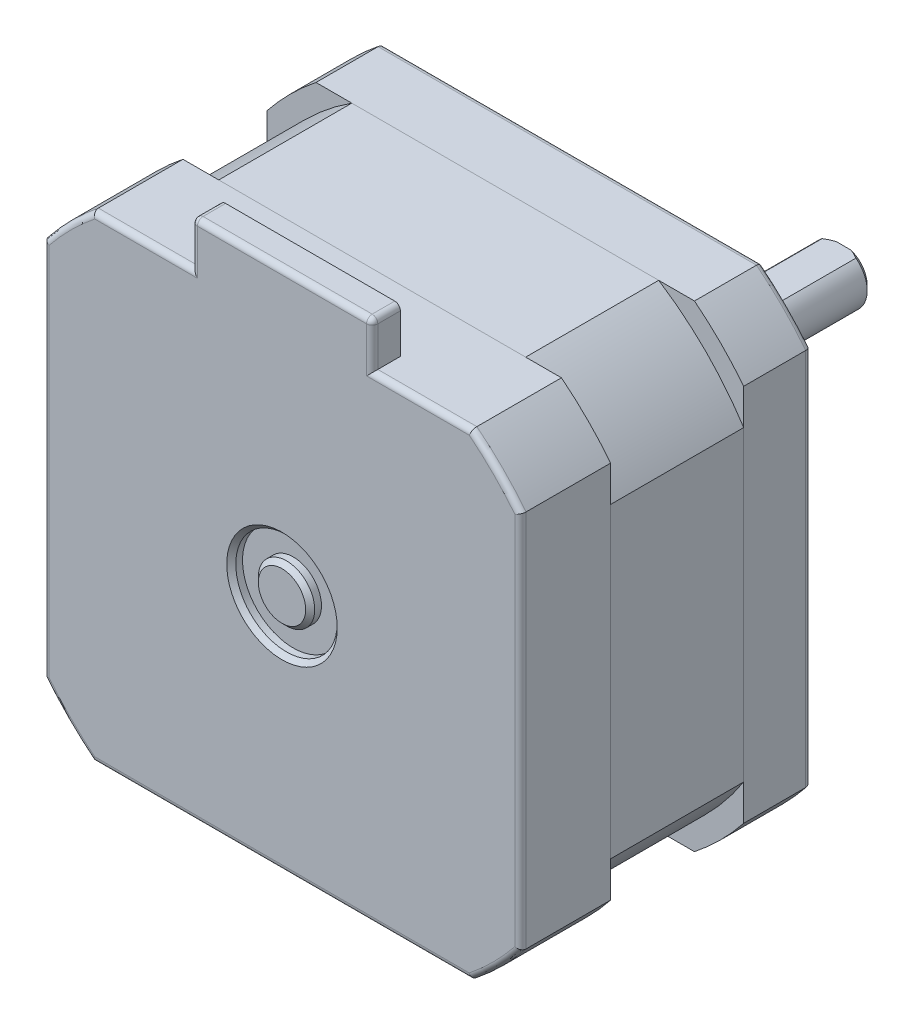
SolidWorks part; units mm, degrees
ref_plane "Plan de face" through (0, 0, 0) normal (0, 0, 1) x (1, 0, 0)
ref_plane "Plan de dessus" through (0, 0, 0) normal (0, 1, 0) x (1, 0, 0)
ref_plane "Plan de droite" through (0, 0, 0) normal (1, 0, 0) x (0, 0, -1)
sketch "Esquisse1" plane through (0, 0, 0) normal (0, 0, 1) x (1, 0, 0)
  line L0 (21.15, 16.7833) -> (21.15, -16.7833)
  line L1 (-21.15, 21.15) -> (21.15, 21.15) construction
  line L2 (-21.15, 21.15) -> (-21.15, -21.15) construction
  line L3 (-21.15, -21.15) -> (21.15, -21.15) construction
  line L4 (21.15, 21.15) -> (21.15, -21.15) construction
  line L5 (-21.15, 21.15) -> (21.15, -21.15) construction
  line L6 (-21.15, -21.15) -> (21.15, 21.15) construction
  line L7 (16.7833, -21.15) -> (-16.7833, -21.15)
  line L8 (-21.15, -16.7833) -> (-21.15, 16.7833)
  line L9 (-16.7833, 21.15) -> (16.7833, 21.15)
  arc A0 (-16.7833, 21.15) -> (-21.15, 16.7833) centre (0, 0) ccw
  arc A1 (21.15, 16.7833) -> (16.7833, 21.15) centre (0, 0) ccw
  arc A2 (-21.15, -16.7833) -> (-16.7833, -21.15) centre (0, 0) ccw
  arc A3 (16.7833, -21.15) -> (21.15, -16.7833) centre (0, 0) ccw
  point P0 (0, 0)
  dimension "D2" = 54
  dimension "D1" = 42.3
extrude "Boss.-Extru.1" add sketch "Esquisse1" along normal blind 6
sketch "Esquisse2" plane through (0, 0, 6) normal (0, 0, 1) x (1, 0, 0)
  line L23 (-13.6088, 21.15) -> (13.6088, 21.15)
  line L24 (16.7833, 21.15) -> (-16.7833, 21.15) construction
  line L25 (21.15, 13.6088) -> (21.15, -13.6088)
  line L26 (21.15, -16.7833) -> (21.15, 16.7833) construction
  line L27 (13.6088, -21.15) -> (-13.6088, -21.15)
  line L28 (-16.7833, -21.15) -> (16.7833, -21.15) construction
  line L29 (-21.15, -13.6088) -> (-21.15, 13.6088)
  line L30 (-21.15, 16.7833) -> (-21.15, -16.7833) construction
  arc A60 (-13.6088, 21.15) -> (-21.15, 13.6088) centre (0, 0) ccw
  arc A61 (21.15, 16.7833) -> (16.7833, 21.15) centre (0, 0) ccw construction
  arc A62 (21.15, 13.6088) -> (13.6088, 21.15) centre (0, 0) ccw
  arc A63 (13.6088, -21.15) -> (21.15, -13.6088) centre (0, 0) ccw
  arc A64 (-21.15, -13.6088) -> (-13.6088, -21.15) centre (0, 0) ccw
  dimension "D1" = 1.85
extrude "Boss.-Extru.2" add sketch "Esquisse2" along normal blind 11.8 separate body
sketch "Esquisse3" plane through (0, 0, 17.8) normal (0, 0, 1) x (1, 0, 0)
  line L0 (-16.7833, -21.15) -> (16.7833, -21.15) construction
  line L1 (21.15, -16.7833) -> (21.15, 16.7833) construction
  line L2 (16.7833, 21.15) -> (-16.7833, 21.15) construction
  line L3 (-21.15, 16.7833) -> (-21.15, -16.7833) construction
  line L4 (-16.7833, -21.15) -> (16.7833, -21.15)
  line L5 (21.15, -16.7833) -> (21.15, 16.7833)
  line L6 (16.7833, 21.15) -> (-16.7833, 21.15)
  line L7 (-21.15, 16.7833) -> (-21.15, -16.7833)
  arc A0 (-21.15, -16.7833) -> (-16.7833, -21.15) centre (0, 0) ccw construction
  arc A1 (16.7833, -21.15) -> (21.15, -16.7833) centre (0, 0) ccw construction
  arc A2 (21.15, 16.7833) -> (16.7833, 21.15) centre (0, 0) ccw construction
  arc A3 (-16.7833, 21.15) -> (-21.15, 16.7833) centre (0, 0) ccw construction
  arc A4 (-21.15, -16.7833) -> (-16.7833, -21.15) centre (0, 0) ccw
  arc A5 (16.7833, -21.15) -> (21.15, -16.7833) centre (0, 0) ccw
  arc A6 (21.15, 16.7833) -> (16.7833, 21.15) centre (0, 0) ccw
  arc A7 (-16.7833, 21.15) -> (-21.15, 16.7833) centre (0, 0) ccw
extrude "Boss.-Extru.3" add sketch "Esquisse3" along normal blind 8 separate body
sketch "Esquisse4" plane through (0, 21.15, 0) normal (0, 1, 0) x (1, 0, 0)
  line L0 (16.7833, -25.8) -> (-16.7833, -25.8) construction
  line L1 (8, -25.8) -> (-8, -25.8)
  line L2 (8, -25.8) -> (8, -23.3)
  line L3 (8, -23.3) -> (-8, -23.3)
  line L4 (-8, -25.8) -> (-8, -23.3)
  line L5 (0, 0) -> (0, -23.3) construction
  dimension "D1" = 2.5
  dimension "D2" = 16
extrude "Boss.-Extru.4" add sketch "Esquisse4" along normal blind 4
sketch "Esquisse5" plane through (0, 0, 0) normal (1, 0, 0) x (0, 0, -1)
  line L0 (0, 0) -> (-78.698, 0) construction
  line L2 (2, 11) -> (0, 11)
  line L3 (2, 11) -> (2, 4.5)
  line L4 (2, 4.5) -> (0, 4.5)
  line L5 (0, 11) -> (0, 4.5)
  line L6 (0, -16.7833) -> (0, 16.7833) construction
  line L7 (24, 0) -> (0, 0)
  line L8 (24, 0) -> (24, 2.5)
  line L9 (24, 2.5) -> (0, 2.5)
  line L10 (0, 0) -> (0, 2.5)
  dimension "D1" = 2
  dimension "D2" = 22
  dimension "D3" = 9
  dimension "D4" = 5
  dimension "D5" = 24
revolve "Révolution1" add sketch "Esquisse5" angle 360 about L0
fillet "Congé1" radius 0.5 14 edges at (-21.15, 0, 25.8) (-19.0919, 19.0919, 25.8) (-12.3916, 21.15, 25.8) (-8, 23.15, 25.8) (0, 25.15, 25.8) (8, 23.15, 25.8) (12.3916, 21.15, 25.8) (19.0919, 19.0919, 25.8) (21.15, 0, 25.8) (19.0919, -19.0919, 25.8) (0, -21.15, 25.8) (-19.0919, -19.0919, 25.8) (-8, 25.15, 24.55) (8, 25.15, 24.55)
fillet "Congé2" radius 0.5 8 edges at (-19.0919, 19.0919, 0) (-21.15, 0, 0) (-19.0919, -19.0919, 0) (0, -21.15, 0) (19.0919, -19.0919, 0) (21.15, 0, 0) (0, 21.15, 0) (19.0919, 19.0919, 0)
chamfer "Chanfrein1" distance 0.4 angle 45 1 edges at (-2.5, 0, -24)
chamfer "Chanfrein2" distance 0.4 angle 45 1 edges at (-4.5, 0, -2)
sketch "Esquisse6" plane through (0, 0, 0) normal (1, 0, 0) x (0, 0, -1)
  line L0 (0, -2.5) -> (23.6, -2.5) construction
  line L1 (24, 2.5) -> (9, 2.5)
  line L2 (24, 2.5) -> (24, 2)
  line L3 (24, 2) -> (9, 2)
  line L4 (9, 2.5) -> (9, 2)
  line L5 (24, -2.1) -> (24, 2.1) construction
  line L6 (23.6, 2.5) -> (0, 2.5) construction
  dimension "D1" = 4.5
  dimension "D2" = 15
extrude "Enlèv. mat.-Extru.1" cut sketch "Esquisse6" against normal through all both and the other way through all
sketch "Esquisse7" plane through (0, 0, 25.8) normal (0, 0, 1) x (1, 0, 0)
  circle A0 centre (0, 0) radius 2.5
  circle A1 centre (0, 0) radius 4.5
  dimension "D1" = 5
  dimension "D2" = 9
extrude "Enlèv. mat.-Extru.2" cut sketch "Esquisse7" against normal blind 1
chamfer "Chanfrein3" distance 0.4 angle 45 2 edges at (4.5, 0, 25.8) (2.5, 0, 25.8)
hole_wizard "Trou taraudé M31" positions "Esquisse8" profile "Esquisse9" tap size "M3" standard "ISO"
sketch "Esquisse8" plane through (0, 0, 0) normal (0, 0, -1) x (-1, 0, 0)
  line L0 (-15.5, 15.5) -> (15.5, 15.5) construction
  line L1 (15.5, 15.5) -> (15.5, -15.5) construction
  line L2 (15.5, -15.5) -> (-15.5, -15.5) construction
  line L3 (-15.5, -15.5) -> (-15.5, 15.5) construction
  circle A0 centre (0, 0) radius 21.9203 construction
  point P5 (-15.5, 15.5)
  point P6 (15.5, 15.5)
  point P7 (15.5, -15.5)
  point P8 (-15.5, -15.5)
  dimension "D1" = 31
sketch "Esquisse9" plane through (15.5, -15.5, 0) normal (1, 0, 0) x (0, 1, 0)
  line L0 (0, 0) -> (0, 5.7511)
  line L1 (0, 5.7511) -> (1.25, 5)
  line L2 (1.25, 5) -> (1.25, 0)
  line L5 (1.25, 0) -> (0, 0)
  line L10 (0, 5.7511) -> (-1.25, 5) construction
  line L11 (0, -6.35) -> (0, 107.95) construction
  dimension "Diamètre du trou pour taraudage" = 2.5
  dimension "Profondeur du trou pour taraudage" = 5
  dimension "Angle de pointe" = 118
cosmetic thread "Filetage de perçage1" parameters "D1"=5, "D2"=3
cosmetic thread "Filetage de perçage2" parameters "D1"=5, "D2"=3
cosmetic thread "Filetage de perçage3" parameters "D1"=5, "D2"=3
cosmetic thread "Filetage de perçage4" parameters "D1"=5, "D2"=3
